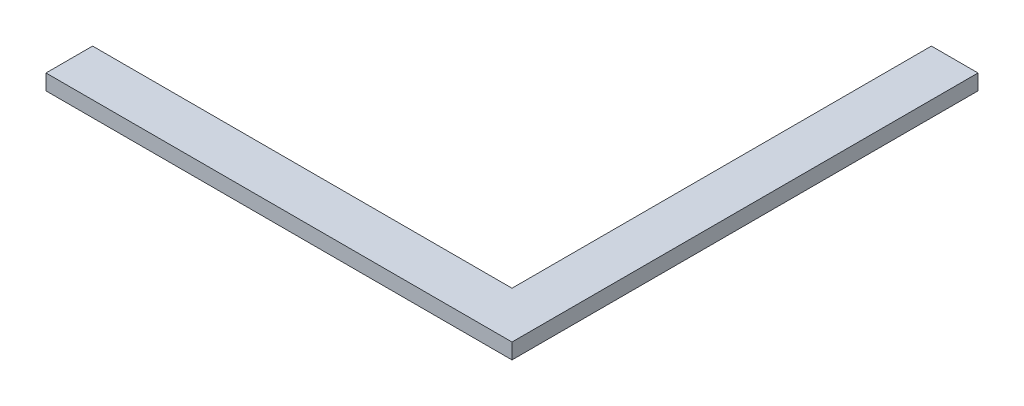
SolidWorks part; units mm, degrees
ref_plane "Front Plane" through (0, 0, 0) normal (0, 0, 1) x (1, 0, 0)
ref_plane "Top Plane" through (0, 0, 0) normal (0, 1, 0) x (1, 0, 0)
ref_plane "Right Plane" through (0, 0, 0) normal (1, 0, 0) x (0, 0, -1)
sketch "Sketch1" plane through (0, 0, 0) normal (0, 1, 0) x (1, 0, 0)
  line L0 (-150, 150) -> (150, -150) construction
  line L1 (-150, 150) -> (150, 150) construction
  line L2 (-150, 150) -> (-150, -150) construction
  line L3 (-150, -150) -> (150, -150) construction
  line L4 (150, 150) -> (150, -150) construction
  line L5 (-150, -150) -> (150, -150)
  line L6 (150, -150) -> (150, 150)
  line L7 (150, 150) -> (120, 150)
  line L8 (120, 150) -> (120, -120)
  line L9 (120, -120) -> (-150, -120)
  line L10 (-150, -120) -> (-150, -150)
  dimension "D1" = 300
  dimension "D2" = 300
  dimension "D3" = 30
  dimension "D4" = 30
extrude "Boss-Extrude1" add sketch "Sketch1" along normal blind 10
